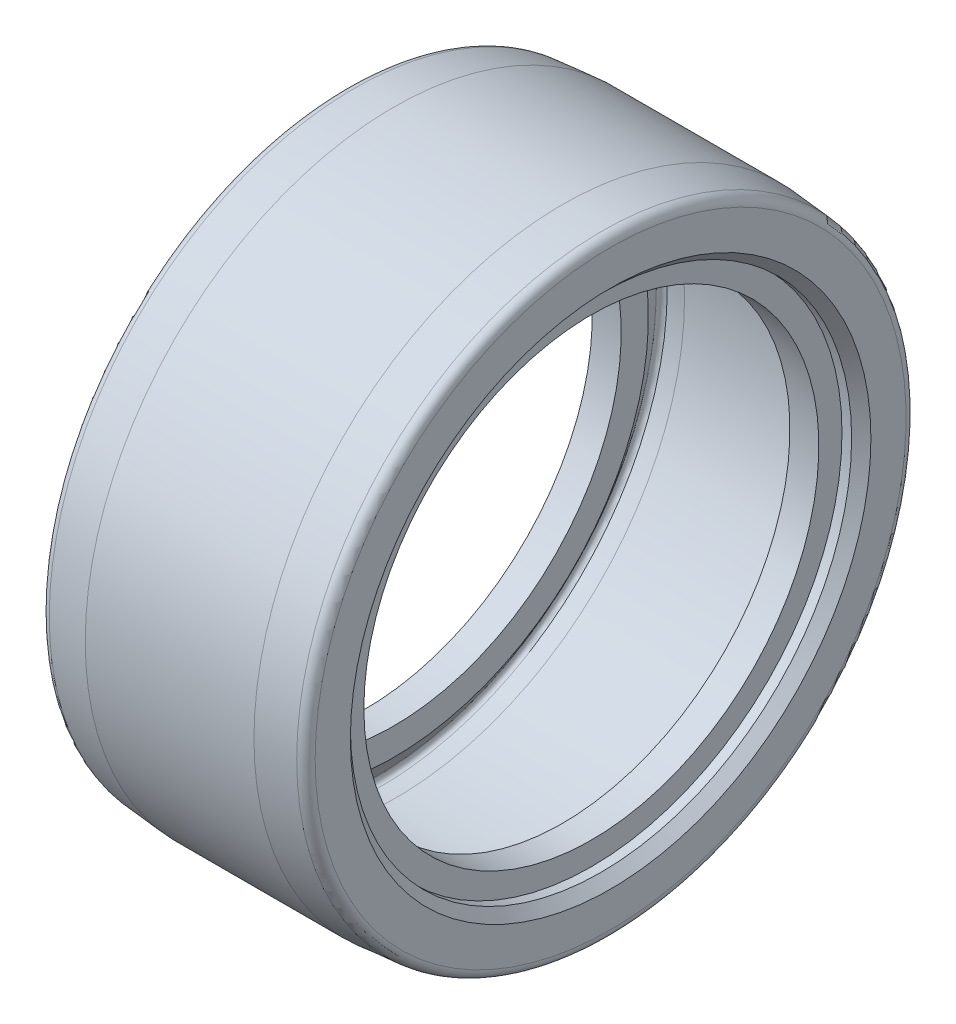
SolidWorks part; units mm, degrees
ref_plane "Plan de face" through (0, 0, 0) normal (0, 0, 1) x (1, 0, 0)
ref_plane "Plan de dessus" through (0, 0, 0) normal (0, 1, 0) x (1, 0, 0)
ref_plane "Plan de droite" through (0, 0, 0) normal (1, 0, 0) x (0, 0, -1)
sketch "Esquisse1" plane through (0, 0, 0) normal (0, 0, 1) x (1, 0, 0)
  line L0 (0, 30.65) -> (0, 27)
  line L1 (5.1732, 30) -> (22.3256, 30)
  line L2 (2, 23.6) -> (5, 23.6)
  line L3 (2, 23.6) -> (25.5, 23.6) construction
  line L4 (2, 23.6) -> (2, 26)
  line L5 (2, 26) -> (1, 26)
  line L6 (5, 32) -> (22.5, 32)
  line L7 (0, 27) -> (1, 26)
  line L8 (1, 26) -> (26.5, 26) construction
  line L9 (22.3256, 30) -> (23.9879, 29.8553)
  line L10 (5, 32) -> (0.9137, 31.6462)
  line L11 (5, 26.4222) -> (3.1495, 29.0722)
  line L12 (22.5, 23.6) -> (22.5, 26.4222)
  line L13 (0, 30.65) -> (27.5, 30.65) construction
  line L14 (5, 23.6) -> (5, 26.4222)
  line L15 (5, 26.4222) -> (22.5, 26.4222) construction
  line L16 (5.1732, 30) -> (3.5163, 29.8566)
  line L17 (0, 0) -> (26.9465, 0) construction
  line L18 (5.1732, 30) -> (0.1745, 29.5672) construction
  line L19 (5, 32) -> (0.0014, 31.5672) construction
  line L20 (22.5, 26.4222) -> (24.3534, 29.0722)
  line L21 (22.5, 32) -> (26.5871, 31.65)
  line L22 (27.5, 27) -> (26.5, 26)
  line L23 (25.5, 26) -> (26.5, 26)
  line L24 (25.5, 23.6) -> (25.5, 26)
  line L25 (25.5, 23.6) -> (22.5, 23.6)
  line L26 (27.5, 30.65) -> (27.5, 27)
  line L27 (0, 0) -> (0, 41.5666) construction
  line L28 (3.1495, 29.0722) -> (24.3534, 29.0722) construction
  arc A0 (0, 30.65) -> (0.9137, 31.6462) centre (1, 30.65) cw
  arc A1 (3.5163, 29.8566) -> (3.1495, 29.0722) centre (3.5595, 29.3584) ccw
  arc A2 (23.9879, 29.8553) -> (24.3534, 29.0722) centre (23.9427, 29.3573) cw
  arc A3 (27.5, 30.65) -> (26.5871, 31.65) centre (26.5, 30.6538) ccw
  dimension "D1" = 23.6
  dimension "D2" = 27.5
  dimension "D3" = 20.5
  dimension "D19" = 0.5
  dimension "D20" = 0.5
  dimension "D4" = 3
  dimension "D5" = 3
  dimension "D6" = 1
  dimension "D7" = 1
  dimension "D8" = 1
  dimension "D9" = 1
  dimension "D10" = 2.4
  dimension "D11" = 1
  dimension "D12" = 2
  dimension "D13" = 0.9962
  dimension "D14" = 17.5
  dimension "D15" = 1
  dimension "D16" = 8.4
  dimension "D17" = 1
  dimension "D18" = 1.35
  dimension "D21" = 1
  dimension "D22" = 2.65
revolve "Révolution1" add sketch "Esquisse1" angle 360 about L17
